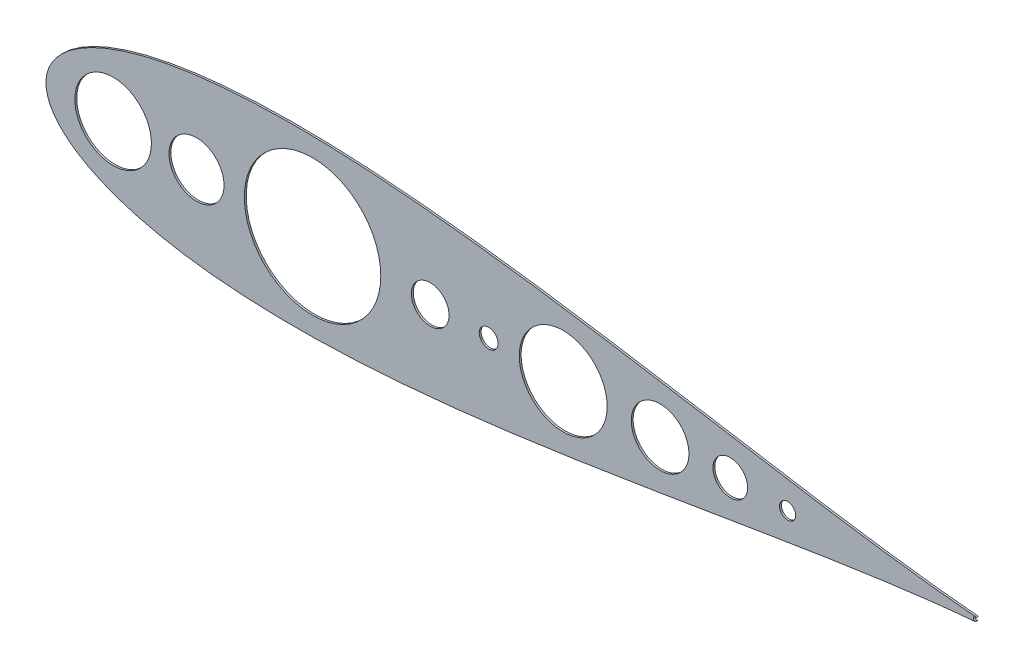
SolidWorks part; units mm, degrees
ref_plane "Front Plane" through (0, 0, 0) normal (0, 0, 1) x (1, 0, 0)
ref_plane "Top Plane" through (0, 0, 0) normal (0, 1, 0) x (1, 0, 0)
ref_plane "Right Plane" through (0, 0, 0) normal (1, 0, 0) x (0, 0, -1)
sketch "Model" plane through (0, 0, 0) normal (0, 0, 1) x (1, 0, 0)
  line L0 (1587.4241, 1059.3175) -> (1587.4241, 1058.8688)
  line L1 (1587.4241, 1058.8688) -> (1586.0864, 1058.8688)
  line L2 (1586.0864, 1058.8688) -> (1585.7232, 1056.4457)
  line L3 (1585.7232, 1056.4457) -> (1585.1805, 1056.4457)
  line L4 (1585.1805, 1056.4457) -> (1585.5437, 1058.8688)
  line L5 (1585.5437, 1058.8688) -> (1584.112, 1058.8688)
  line L6 (1584.112, 1058.8688) -> (1583.7488, 1056.4457)
  line L7 (1583.7488, 1056.4457) -> (1583.2062, 1056.4457)
  line L8 (1583.2062, 1056.4457) -> (1583.5693, 1058.8688)
  line L9 (1583.5693, 1058.8688) -> (1582.3985, 1058.8688)
  line L10 (1582.3985, 1058.8688) -> (1582.3985, 1059.3175)
  line L11 (1582.3985, 1059.3175) -> (1583.6366, 1059.3175)
  line L12 (1583.6366, 1059.3175) -> (1583.8792, 1060.9329)
  line L13 (1583.8792, 1060.9329) -> (1582.578, 1060.9329)
  line L14 (1582.578, 1060.9329) -> (1582.578, 1061.3816)
  line L15 (1582.578, 1061.3816) -> (1583.9465, 1061.3816)
  line L16 (1583.9465, 1061.3816) -> (1584.2831, 1063.6252)
  line L17 (1584.2831, 1063.6252) -> (1584.8244, 1063.6252)
  line L18 (1584.8244, 1063.6252) -> (1584.4878, 1061.3816)
  line L19 (1584.4878, 1061.3816) -> (1585.9209, 1061.3816)
  line L20 (1585.9209, 1061.3816) -> (1586.2574, 1063.6252)
  line L21 (1586.2574, 1063.6252) -> (1586.7987, 1063.6252)
  line L22 (1586.7987, 1063.6252) -> (1586.4622, 1061.3816)
  line L23 (1586.4622, 1061.3816) -> (1587.6036, 1061.3816)
  line L24 (1587.6036, 1061.3816) -> (1587.6036, 1060.9329)
  line L25 (1587.6036, 1060.9329) -> (1586.3949, 1060.9329)
  line L26 (1586.3949, 1060.9329) -> (1586.1537, 1059.3175)
  line L27 (1586.1537, 1059.3175) -> (1587.4241, 1059.3175)
  line L28 (1585.8536, 1060.9329) -> (1584.4205, 1060.9329)
  line L29 (1584.4205, 1060.9329) -> (1584.1793, 1059.3175)
  line L30 (1584.1793, 1059.3175) -> (1585.611, 1059.3175)
  line L31 (1585.611, 1059.3175) -> (1585.8536, 1060.9329)
  line L32 (1589.6677, 1061.2919) -> (1589.0395, 1061.2919)
  line L33 (1589.0395, 1061.2919) -> (1589.0563, 1061.5415)
  line L34 (1589.0563, 1061.5415) -> (1589.0928, 1061.7799)
  line L35 (1589.0928, 1061.7799) -> (1589.1475, 1062.0056)
  line L36 (1589.1475, 1062.0056) -> (1589.2232, 1062.2216)
  line L37 (1589.2232, 1062.2216) -> (1589.3171, 1062.4249)
  line L38 (1589.3171, 1062.4249) -> (1589.4307, 1062.6184)
  line L39 (1589.4307, 1062.6184) -> (1589.5639, 1062.7993)
  line L40 (1589.5639, 1062.7993) -> (1589.7168, 1062.969)
  line L41 (1589.7168, 1062.969) -> (1589.8836, 1063.1232)
  line L42 (1589.8836, 1063.1232) -> (1590.0617, 1063.2564)
  line L43 (1590.0617, 1063.2564) -> (1590.2482, 1063.3686)
  line L44 (1590.2482, 1063.3686) -> (1590.4431, 1063.4612)
  line L45 (1590.4431, 1063.4612) -> (1590.6493, 1063.5327)
  line L46 (1590.6493, 1063.5327) -> (1590.8638, 1063.5846)
  line L47 (1590.8638, 1063.5846) -> (1591.0882, 1063.6154)
  line L48 (1591.0882, 1063.6154) -> (1591.3223, 1063.6252)
  line L49 (1591.3223, 1063.6252) -> (1591.5523, 1063.6154)
  line L50 (1591.5523, 1063.6154) -> (1591.7725, 1063.586)
  line L51 (1591.7725, 1063.586) -> (1591.98, 1063.5383)
  line L52 (1591.98, 1063.5383) -> (1592.1777, 1063.471)
  line L53 (1592.1777, 1063.471) -> (1592.3628, 1063.3826)
  line L54 (1592.3628, 1063.3826) -> (1592.5367, 1063.2761)
  line L55 (1592.5367, 1063.2761) -> (1592.7008, 1063.1513)
  line L56 (1592.7008, 1063.1513) -> (1592.8522, 1063.0054)
  line L57 (1592.8522, 1063.0054) -> (1592.9896, 1062.847)
  line L58 (1592.9896, 1062.847) -> (1593.1074, 1062.6815)
  line L59 (1593.1074, 1062.6815) -> (1593.2084, 1062.509)
  line L60 (1593.2084, 1062.509) -> (1593.2911, 1062.331)
  line L61 (1593.2911, 1062.331) -> (1593.3542, 1062.1445)
  line L62 (1593.3542, 1062.1445) -> (1593.4005, 1061.951)
  line L63 (1593.4005, 1061.951) -> (1593.4271, 1061.7518)
  line L64 (1593.4271, 1061.7518) -> (1593.4369, 1061.5443)
  line L65 (1593.4369, 1061.5443) -> (1593.4187, 1061.2526)
  line L66 (1593.4187, 1061.2526) -> (1593.364, 1060.9708)
  line L67 (1593.364, 1060.9708) -> (1593.2743, 1060.6988)
  line L68 (1593.2743, 1060.6988) -> (1593.1467, 1060.4351)
  line L69 (1593.1467, 1060.4351) -> (1593.0653, 1060.3005)
  line L70 (1593.0653, 1060.3005) -> (1592.9672, 1060.1533)
  line L71 (1592.9672, 1060.1533) -> (1592.8522, 1059.9948)
  line L72 (1592.8522, 1059.9948) -> (1592.7204, 1059.8266)
  line L73 (1592.7204, 1059.8266) -> (1592.5703, 1059.6443)
  line L74 (1592.5703, 1059.6443) -> (1592.4049, 1059.4522)
  line L75 (1592.4049, 1059.4522) -> (1592.2212, 1059.2488)
  line L76 (1592.2212, 1059.2488) -> (1592.0207, 1059.0329)
  line L77 (1592.0207, 1059.0329) -> (1590.2693, 1057.1637)
  line L78 (1590.2693, 1057.1637) -> (1593.5267, 1057.1637)
  line L79 (1593.5267, 1057.1637) -> (1593.5267, 1056.4457)
  line L80 (1593.5267, 1056.4457) -> (1588.7703, 1056.4457)
  line L81 (1588.7703, 1056.4457) -> (1591.485, 1059.3428)
  line L82 (1591.485, 1059.3428) -> (1591.6827, 1059.5503)
  line L83 (1591.6827, 1059.5503) -> (1591.8622, 1059.7438)
  line L84 (1591.8622, 1059.7438) -> (1592.0235, 1059.9233)
  line L85 (1592.0235, 1059.9233) -> (1592.1665, 1060.0888)
  line L86 (1592.1665, 1060.0888) -> (1592.2913, 1060.2416)
  line L87 (1592.2913, 1060.2416) -> (1592.3993, 1060.379)
  line L88 (1592.3993, 1060.379) -> (1592.4876, 1060.5038)
  line L89 (1592.4876, 1060.5038) -> (1592.5591, 1060.6146)
  line L90 (1592.5591, 1060.6146) -> (1592.6685, 1060.825)
  line L91 (1592.6685, 1060.825) -> (1592.747, 1061.0409)
  line L92 (1592.747, 1061.0409) -> (1592.7933, 1061.2611)
  line L93 (1592.7933, 1061.2611) -> (1592.8087, 1061.4882)
  line L94 (1592.8087, 1061.4882) -> (1592.8017, 1061.6312)
  line L95 (1592.8017, 1061.6312) -> (1592.7807, 1061.7687)
  line L96 (1592.7807, 1061.7687) -> (1592.747, 1061.9005)
  line L97 (1592.747, 1061.9005) -> (1592.6994, 1062.0281)
  line L98 (1592.6994, 1062.0281) -> (1592.6362, 1062.1515)
  line L99 (1592.6362, 1062.1515) -> (1592.5605, 1062.2679)
  line L100 (1592.5605, 1062.2679) -> (1592.4722, 1062.38)
  line L101 (1592.4722, 1062.38) -> (1592.3684, 1062.488)
  line L102 (1592.3684, 1062.488) -> (1592.2548, 1062.5862)
  line L103 (1592.2548, 1062.5862) -> (1592.1356, 1062.6717)
  line L104 (1592.1356, 1062.6717) -> (1592.0108, 1062.7432)
  line L105 (1592.0108, 1062.7432) -> (1591.879, 1062.8021)
  line L106 (1591.879, 1062.8021) -> (1591.7402, 1062.8484)
  line L107 (1591.7402, 1062.8484) -> (1591.5972, 1062.8806)
  line L108 (1591.5972, 1062.8806) -> (1591.4471, 1062.9003)
  line L109 (1591.4471, 1062.9003) -> (1591.2901, 1062.9073)
  line L110 (1591.2901, 1062.9073) -> (1591.126, 1062.9003)
  line L111 (1591.126, 1062.9003) -> (1590.969, 1062.8806)
  line L112 (1590.969, 1062.8806) -> (1590.8189, 1062.847)
  line L113 (1590.8189, 1062.847) -> (1590.6759, 1062.8007)
  line L114 (1590.6759, 1062.8007) -> (1590.5399, 1062.7418)
  line L115 (1590.5399, 1062.7418) -> (1590.4109, 1062.6689)
  line L116 (1590.4109, 1062.6689) -> (1590.2889, 1062.582)
  line L117 (1590.2889, 1062.582) -> (1590.1739, 1062.4824)
  line L118 (1590.1739, 1062.4824) -> (1590.0687, 1062.3716)
  line L119 (1590.0687, 1062.3716) -> (1589.9762, 1062.2496)
  line L120 (1589.9762, 1062.2496) -> (1589.8949, 1062.1164)
  line L121 (1589.8949, 1062.1164) -> (1589.8248, 1061.9734)
  line L122 (1589.8248, 1061.9734) -> (1589.7673, 1061.8191)
  line L123 (1589.7673, 1061.8191) -> (1589.7224, 1061.6537)
  line L124 (1589.7224, 1061.6537) -> (1589.6887, 1061.4784)
  line L125 (1589.6887, 1061.4784) -> (1589.6677, 1061.2919)
  circle A0 centre (590.5325, 1063.59) radius 51.5724
  circle A1 centre (1017.874, 1063.59) radius 25.4
  circle A2 centre (1327.6902, 1063.59) radius 38.8399
  circle A3 centre (1197.1176, 1063.59) radius 59.2339
  circle A4 centre (859.292, 1063.59) radius 91.9633
  circle A5 centre (1499.5197, 1063.59) radius 10.8856
  arc A6 (1753.5915, 1065.7761) -> (1753.5915, 1061.4039) centre (1752.3747, 1063.59) ccw
  circle A7 centre (702.914, 1063.59) radius 37.084
  circle A8 centre (1422.2718, 1063.59) radius 23.3715
  circle A9 centre (1096.614, 1063.59) radius 12.7
  arc A10 (1753.5915, 1065.7761) -> (1751.6604, 1066.6718) centre (1751.4042, 1063.59) ccw
  arc A11 (1751.6604, 1060.5082) -> (1753.5915, 1061.4039) centre (1751.4042, 1063.59) ccw
  spline S0 degree 3 poles (1751.6604, 1066.6718) (1750.6524, 1066.7556) (1743.0559, 1067.3955) (1728.0954, 1068.7783) (1705.8888, 1071.0883) (1681.2678, 1073.923) (1654.3249, 1077.2993) (1625.1858, 1081.2206) (1593.9765, 1085.6782) (1560.8322, 1090.649) (1525.8937, 1096.0977) (1489.3072, 1101.9756) (1451.224, 1108.2219) (1411.7997, 1114.7648) (1371.1938, 1121.5216) (1329.5693, 1128.4006) (1287.0926, 1135.3022) (1243.9334, 1142.1202) (1200.2644, 1148.7439) (1156.2614, 1155.0592) (1112.1035, 1160.9507) (1067.9727, 1166.3036) (1024.0541, 1171.0051) (980.5363, 1174.9467) (937.6107, 1178.0256) (895.4723, 1180.1469) (854.3187, 1181.2249) (814.351, 1181.1848) (775.7732, 1179.9633) (738.7925, 1177.5125) (703.6198, 1173.7967) (670.4701, 1168.7994) (639.5645, 1162.5187) (611.1315, 1154.9756) (585.4116, 1146.2144) (562.6612, 1136.3131) (543.1568, 1125.4029) (527.1897, 1113.7051) (515.0287, 1101.6017) (506.7955, 1089.7329) (502.2044, 1079.0248) (500.3505, 1070.4349) (499.9282, 1063.59) (500.3505, 1056.7451) (502.2044, 1048.1552) (506.7955, 1037.4472) (515.0287, 1025.5783) (527.1897, 1013.475) (543.1568, 1001.7771) (562.6612, 990.8669) (585.4116, 980.9656) (611.1315, 972.2044) (639.5645, 964.6613) (670.4701, 958.3806) (703.6198, 953.3833) (738.7925, 949.6675) (775.7732, 947.2167) (814.351, 945.9952) (854.3187, 945.9551) (895.4723, 947.0331) (937.6107, 949.1544) (980.5363, 952.2334) (1024.0541, 956.1749) (1067.9727, 960.8764) (1112.1035, 966.2293) (1156.2614, 972.1208) (1200.2644, 978.4361) (1243.9334, 985.0598) (1287.0926, 991.8778) (1329.5693, 998.7794) (1371.1938, 1005.6584) (1411.7997, 1012.4152) (1451.224, 1018.9581) (1489.3072, 1025.2044) (1525.8937, 1031.0823) (1560.8322, 1036.531) (1593.9765, 1041.5018) (1625.1858, 1045.9594) (1654.3249, 1049.8807) (1681.2678, 1053.257) (1705.8888, 1056.0917) (1728.0954, 1058.4017) (1743.0559, 1059.7845) (1750.6524, 1060.4244) (1751.6604, 1060.5082) knots 0.020157 0.020157 0.020157 0.020157 0.021271 0.028553 0.036781 0.04592 0.055932 0.066773 0.078397 0.090755 0.103793 0.117456 0.131686 0.146422 0.1616 0.177156 0.193024 0.209135 0.225421 0.241812 0.258238 0.274629 0.290914 0.307025 0.322893 0.338448 0.353626 0.368361 0.38259 0.396253 0.40929 0.421647 0.43327 0.444109 0.454119 0.463255 0.471479 0.478755 0.485052 0.490344 0.49461 0.497833 0.5 0.502167 0.50539 0.509656 0.514948 0.521245 0.528521 0.536745 0.545881 0.555891 0.56673 0.578353 0.59071 0.603747 0.61741 0.631639 0.646374 0.661552 0.677107 0.692975 0.709086 0.725371 0.741762 0.758188 0.774579 0.790865 0.806976 0.822844 0.8384 0.853578 0.868314 0.882544 0.896207 0.909245 0.921603 0.933227 0.944068 0.95408 0.963219 0.971447 0.978729 0.979843 0.979843 0.979843 0.979843
sketch "Sketch3" plane through (0, 0, 0) normal (0, 0, 1) x (1, 0, 0)
  circle A0 centre (590.5325, 1063.59) radius 51.5724
  circle A1 centre (1017.874, 1063.59) radius 25.4
  circle A2 centre (1327.6902, 1063.59) radius 38.8399
  circle A3 centre (1197.1176, 1063.59) radius 59.2339
  circle A4 centre (859.292, 1063.59) radius 91.9633
  circle A5 centre (1499.5197, 1063.59) radius 10.8856
  arc A6 (1753.5915, 1065.7761) -> (1753.5915, 1061.4039) centre (1752.3747, 1063.59) ccw
  circle A7 centre (702.914, 1063.59) radius 37.084
  circle A8 centre (1422.2718, 1063.59) radius 23.3715
  circle A9 centre (1096.614, 1063.59) radius 12.7
  arc A10 (1753.5915, 1065.7761) -> (1751.6604, 1066.6718) centre (1751.4042, 1063.59) ccw
  arc A11 (1751.6604, 1060.5082) -> (1753.5915, 1061.4039) centre (1751.4042, 1063.59) ccw
  spline S0 degree 3 poles (1751.6604, 1066.6718) (1750.6524, 1066.7556) (1743.0559, 1067.3955) (1728.0954, 1068.7783) (1705.8888, 1071.0883) (1681.2678, 1073.923) (1654.3249, 1077.2993) (1625.1858, 1081.2206) (1593.9765, 1085.6782) (1560.8322, 1090.649) (1525.8937, 1096.0977) (1489.3072, 1101.9756) (1451.224, 1108.2219) (1411.7997, 1114.7648) (1371.1938, 1121.5216) (1329.5693, 1128.4006) (1287.0926, 1135.3022) (1243.9334, 1142.1202) (1200.2644, 1148.7439) (1156.2614, 1155.0592) (1112.1035, 1160.9507) (1067.9727, 1166.3036) (1024.0541, 1171.0051) (980.5363, 1174.9467) (937.6107, 1178.0256) (895.4723, 1180.1469) (854.3187, 1181.2249) (814.351, 1181.1848) (775.7732, 1179.9633) (738.7925, 1177.5125) (703.6198, 1173.7967) (670.4701, 1168.7994) (639.5645, 1162.5187) (611.1315, 1154.9756) (585.4116, 1146.2144) (562.6612, 1136.3131) (543.1568, 1125.4029) (527.1897, 1113.7051) (515.0287, 1101.6017) (506.7955, 1089.7329) (502.2044, 1079.0248) (500.3505, 1070.4349) (499.9282, 1063.59) (500.3505, 1056.7451) (502.2044, 1048.1552) (506.7955, 1037.4472) (515.0287, 1025.5783) (527.1897, 1013.475) (543.1568, 1001.7771) (562.6612, 990.8669) (585.4116, 980.9656) (611.1315, 972.2044) (639.5645, 964.6613) (670.4701, 958.3806) (703.6198, 953.3833) (738.7925, 949.6675) (775.7732, 947.2167) (814.351, 945.9952) (854.3187, 945.9551) (895.4723, 947.0331) (937.6107, 949.1544) (980.5363, 952.2334) (1024.0541, 956.1749) (1067.9727, 960.8764) (1112.1035, 966.2293) (1156.2614, 972.1208) (1200.2644, 978.4361) (1243.9334, 985.0598) (1287.0926, 991.8778) (1329.5693, 998.7794) (1371.1938, 1005.6584) (1411.7997, 1012.4152) (1451.224, 1018.9581) (1489.3072, 1025.2044) (1525.8937, 1031.0823) (1560.8322, 1036.531) (1593.9765, 1041.5018) (1625.1858, 1045.9594) (1654.3249, 1049.8807) (1681.2678, 1053.257) (1705.8888, 1056.0917) (1728.0954, 1058.4017) (1743.0559, 1059.7845) (1750.6524, 1060.4244) (1751.6604, 1060.5082) knots 0.020157 0.020157 0.020157 0.020157 0.021271 0.028553 0.036781 0.04592 0.055932 0.066773 0.078397 0.090755 0.103793 0.117456 0.131686 0.146422 0.1616 0.177156 0.193024 0.209135 0.225421 0.241812 0.258238 0.274629 0.290914 0.307025 0.322893 0.338448 0.353626 0.368361 0.38259 0.396253 0.40929 0.421647 0.43327 0.444109 0.454119 0.463255 0.471479 0.478755 0.485052 0.490344 0.49461 0.497833 0.5 0.502167 0.50539 0.509656 0.514948 0.521245 0.528521 0.536745 0.545881 0.555891 0.56673 0.578353 0.59071 0.603747 0.61741 0.631639 0.646374 0.661552 0.677107 0.692975 0.709086 0.725371 0.741762 0.758188 0.774579 0.790865 0.806976 0.822844 0.8384 0.853578 0.868314 0.882544 0.896207 0.909245 0.921603 0.933227 0.944068 0.95408 0.963219 0.971447 0.978729 0.979843 0.979843 0.979843 0.979843
extrude "Boss-Extrude1" add sketch "Sketch3" along normal blind 2.54
